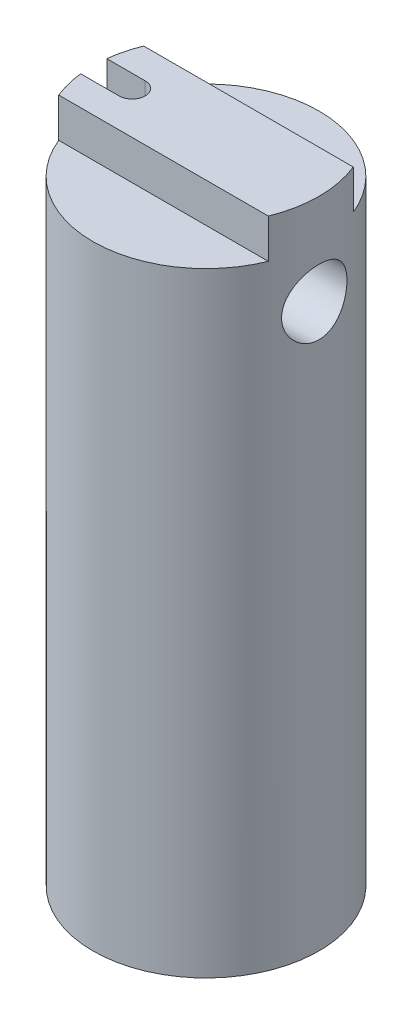
SolidWorks part; units mm, degrees
material "AISI 1020"
ref_plane "Спереди" through (0, 0, 0) normal (0, 0, 1) x (1, 0, 0)
ref_plane "Сверху" through (0, 0, 0) normal (0, 1, 0) x (1, 0, 0)
ref_plane "Справа" through (0, 0, 0) normal (1, 0, 0) x (0, 0, -1)
sketch "Эскиз1" plane through (0, 0, 0) normal (0, 1, 0) x (1, 0, 0)
  circle A0 centre (0, 0) radius 8.65 construction
  circle A1 centre (0, 0) radius 8.65
extrude "Бобышка-Вытянуть1" add sketch "Эскиз1" against normal blind 50
sketch "Эскиз2" plane through (0, -50, 0) normal (0, -1, 0) x (1, 0, 0)
  line L0 (-5.65, 0) -> (-8.65, 0) construction
  line L1 (0.0148, 0) -> (-17.0651, 0) construction
  line L2 (-5.65, -3) -> (-8.65, -3)
  line L3 (-5.65, 3) -> (-8.65, 3)
  circle A0 centre (0, 0) radius 8.65 construction
  arc A1 (-5.65, -3) -> (-5.65, 3) centre (-5.65, 0) ccw
  arc A2 (-8.65, 3) -> (-8.65, -3) centre (-8.65, 0) ccw
  point P7 (-7.15, 0)
  dimension "D1" = 6
  dimension "D2" = 3
extrude "Вырез-Вытянуть1" cut sketch "Эскиз2" against normal up to vertex (40 mm away)
sketch "Эскиз3" plane through (0, 0, 0) normal (0, -1, 0) x (1, 0, 0)
  line L0 (-5.65, 0) -> (-8.65, 0) construction
  line L1 (-36.3091, 0) -> (-5.65, 0) construction
  line L2 (-5.65, -1) -> (-8.65, -1)
  line L3 (-5.65, 1) -> (-8.65, 1)
  arc A1 (-5.65, -1) -> (-5.65, 1) centre (-5.65, 0) ccw
  arc A2 (-8.65, 1) -> (-8.65, -1) centre (-8.65, 0) ccw
  arc A3 (-5.65, -3) -> (-5.65, 3) centre (-5.65, 0) ccw construction
  circle A4 centre (0, 0) radius 8.65 construction
  point P7 (-7.15, 0)
  dimension "D1" = 2
extrude "Вырез-Вытянуть2" cut sketch "Эскиз3" along normal through all
sketch "Эскиз4" plane through (0, 0, 0) normal (1, 0, 0) x (0, 0, -1)
  line L0 (0, -1000) -> (0, 49000) construction
  line L1 (3.25, -3) -> (3.25, 0)
  line L2 (-3.25, -3) -> (-10.65, -3)
  line L3 (-3.25, -3) -> (-3.25, 0)
  line L4 (-3.25, 0) -> (-10.65, 0)
  line L5 (-10.65, -3) -> (-10.65, 0)
  line L6 (3.25, 0) -> (10.65, 0)
  line L7 (10.65, -3) -> (10.65, 0)
  line L8 (3.25, -3) -> (10.65, -3)
  line L9 (8.65, 0) -> (-8.65, 0) construction
  line L10 (-8.65, 0) -> (-8.65, -50) construction
  dimension "D1" = 2
extrude "Вырез-Вытянуть3" cut sketch "Эскиз4" against normal through all both and the other way through all
ref_plane "Плоскость1" through (8.65, 0, 0) normal (1, 0, 0) x (0, 0, -1)
sketch "Эскиз5" plane through (8.65, 0, 0) normal (1, 0, 0) x (0, 0, -1)
  line L0 (0, 13.3669) -> (0, -38.2097) construction
  line L1 (-7.5904, -13) -> (7.5904, -13) construction
  circle A0 centre (0, -7) radius 3
  dimension "D1" = 6
  dimension "D2" = 6
hole_wizard "Отверстие обработанное метчиком M61" positions "Эскиз6" profile "Эскиз7" tap size "M6" standard "ISO"
sketch "Эскиз6" plane through (8.65, 0, 0) normal (1, 0, 0) x (0, 0, -1)
  point P0 (0, -7)
sketch "Эскиз7" plane through (8.65, -7, 0) normal (0, 1, 0) x (0, 0, -1)
  line L0 (0, 0) -> (0, 6.5022)
  line L1 (0, 6.5022) -> (2.5, 5)
  line L2 (2.5, 5) -> (2.5, 0)
  line L5 (2.5, 0) -> (0, 0)
  line L10 (0, 6.5022) -> (-2.5, 5) construction
  line L11 (0, -6.35) -> (0, 107.95) construction
  dimension "Диаметр сверла" = 5
  dimension "Глубина сверла" = 5
  dimension "Угол заточки сверла" = 118
cosmetic thread "Отверстие резьбы1" parameters "D1"=5, "D2"=6
